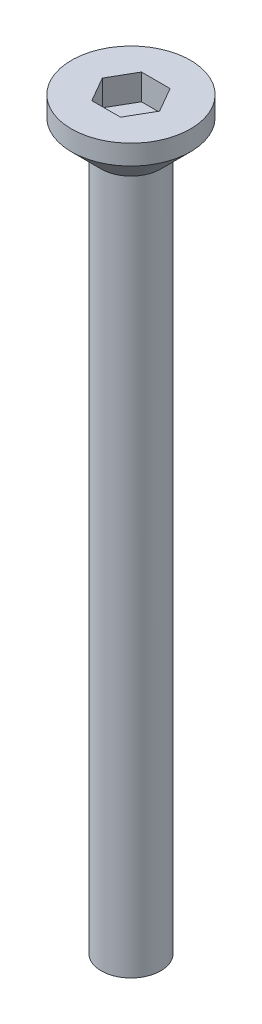
SolidWorks part; units mm, degrees
material "AISI 304"
ref_plane "前视基准面" through (0, 0, 0) normal (0, 0, 1) x (1, 0, 0)
ref_plane "上视基准面" through (0, 0, 0) normal (0, 1, 0) x (1, 0, 0)
ref_plane "右视基准面" through (0, 0, 0) normal (1, 0, 0) x (0, 0, -1)
sketch "草图1" plane through (0, 0, 0) normal (0, 1, 0) x (1, 0, 0)
  circle A0 centre (0, 0) radius 3
  dimension "D1" = 6
extrude "沉头头" add sketch "草图1" along normal blind 2.5
chamfer "倒角1" distance 1.5 angle 45 1 edges at (0, 0, 3)
sketch "草图2" plane through (0, 2.5, 0) normal (0, 1, 0) x (1, 0, 0)
  line L1 (1.4434, 0) -> (0.7217, 1.25)
  line L2 (0.7217, 1.25) -> (-0.7217, 1.25)
  line L3 (-0.7217, 1.25) -> (-1.4434, 0)
  line L4 (-1.4434, 0) -> (-0.7217, -1.25)
  line L5 (-0.7217, -1.25) -> (0.7217, -1.25)
  line L6 (0.7217, -1.25) -> (1.4434, 0)
  circle A0 centre (0, 0) radius 1.25 construction
  dimension "D1" = 2.5
extrude "内六角口" cut sketch "草图2" against normal blind 1.3
sketch "草图3" plane through (0, 0, 0) normal (0, -1, 0) x (1, 0, 0)
  circle A0 centre (0, 0) radius 1.5
  dimension "D1" = 3
extrude "螺纹长" add sketch "草图3" along normal blind 35
